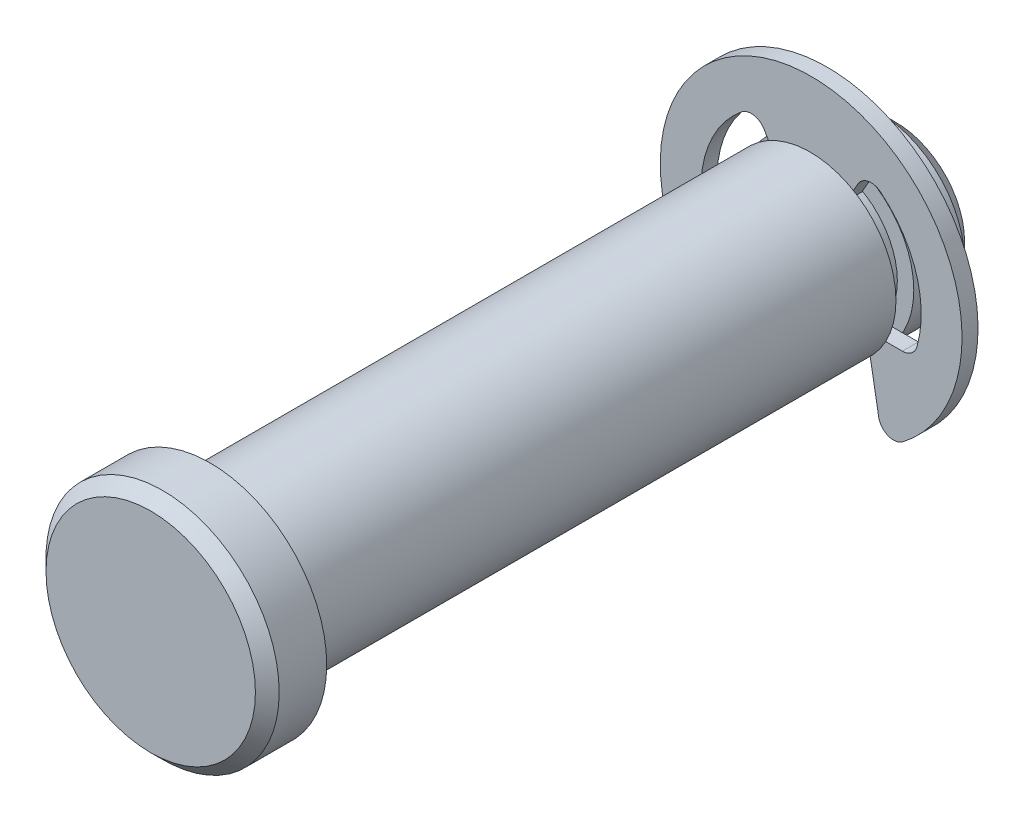
SolidWorks part; units mm, degrees
ref_plane "Front" through (0, 0, 0) normal (0, 0, 1) x (1, 0, 0)
ref_plane "Top" through (0, 0, 0) normal (0, 1, 0) x (1, 0, 0)
ref_plane "Right" through (0, 0, 0) normal (1, 0, 0) x (0, 0, -1)
sketch "Sketch2" plane through (0, 0, 0) normal (0, 0, 1) x (1, 0, 0)
  circle A0 centre (0, 0) radius 4.7625
  point P3 (0, 4.7625)
  point P4 (0, -4.7625)
  dimension "dia" = 9.525
extrude "Extrude1" add sketch "Sketch2" along normal mid plane 38.1
sketch "Sketch3" plane through (0, 0, 0) normal (1, 0, 0) x (0, 0, -1)
  line L0 (19.05, 4.7625) -> (-19.05, 4.7625) construction
  line L1 (14.2875, 4.7625) -> (15.2781, 4.7625)
  line L2 (14.2875, 4.7625) -> (14.2875, 3.8481)
  line L3 (14.2875, 3.8481) -> (15.2781, 3.8481)
  line L4 (15.2781, 4.7625) -> (15.2781, 3.8481)
  line L5 (-19.05, 4.7625) -> (-19.05, -4.7625) construction
  line L10 (15.2781, 3.8481) -> (15.2781, -3.8481) construction
  point P11 (15.2781, 0)
  point P14 (14.7828, 4.7625)
  dimension "groove wd" = 0.9906
  dimension "groove dia" = 7.6962
  dimension "usable lg" = 33.3375
revolve "Cut-Revolve1" cut sketch "Sketch3" angle 360 about axis through (0, 0, 19.05) along (0, 0, -1)
sketch "Sketch8" plane through (0, 0, 19.05) normal (0, 0, 1) x (1, 0, 0)
  circle A0 centre (0, 0) radius 6.477
  dimension "head dia" = 12.954
extrude "Extrude6" add sketch "Sketch8" along normal blind 3.302
chamfer "Chamfer2" distance 0.6604 angle 45 1 edges at (6.477, 0, 22.352)
ref_plane "Plane1" through (0, 0, -14.7828) normal (0, 0, 1) x (1, 0, 0)
sketch "Sketch4" plane through (0, 0, -14.7828) normal (0, 0, 1) x (1, 0, 0)
  line L0 (0, 3.8481) -> (0, -3.8481) construction
  circle A0 centre (0, 0) radius 8.382
  circle A1 centre (0, 0) radius 3.8481
  dimension "ring dia" = 16.764
extrude "Extrude2" add sketch "Sketch4" along normal mid plane 0.889 separate body
sketch "Sketch5" plane through (0, 0, 0) normal (0, 0, 1) x (1, 0, 0)
  line L0 (0, 8.382) -> (0, 3.8481) construction
  line L1 (-3.0575, 5.2958) -> (0, 0)
  line L2 (-5.6624, -2.3089) -> (-3.0785, -2.3089)
  line L3 (0, 0) -> (3.0575, 5.2958)
  line L4 (-3.0785, -2.3089) -> (-3.9728, -7.3807)
  line L5 (3.0785, -2.3089) -> (3.9728, -7.3807)
  line L6 (3.0785, -2.3089) -> (5.6624, -2.3089)
  arc A0 (-3.0575, 5.2958) -> (-5.6624, -2.3089) centre (0, 0) ccw
  circle A1 centre (0, 0) radius 8.382 construction
  circle A2 centre (0, 0) radius 3.8481 construction
  arc A3 (5.6624, -2.3089) -> (3.0575, 5.2958) centre (0, 0) ccw
  arc A4 (-3.9728, -7.3807) -> (3.9728, -7.3807) centre (0, 0) ccw
  circle A5 centre (0, 0) radius 3.8481 construction
  point P10 (0, 6.1151)
  dimension "D1" = 30
  dimension "D2" = 10
  dimension "D3" = 2.3089
extrude "Extrude4" cut sketch "Sketch5" against normal through all
sketch "Sketch6" plane through (0, 0, -14.3383) normal (0, 0, 1) x (1, 0, 0)
  line L0 (-1.9241, 3.3326) -> (1.9241, 3.3326)
  circle A0 centre (0, 0) radius 3.8481 construction
  arc A1 (1.9241, 3.3326) -> (-1.9241, 3.3326) centre (0, 0) ccw
extrude "Extrude5" add sketch "Sketch6" against normal up to surface (0.889 mm away) up to face at (0, 1.0514, -15.2273)
fillet "Fillet1" radius 0.8382 6 edges at (3.9728, -7.3807, -14.7828) (-3.9728, -7.3807, -14.7828) (5.6624, -2.3089, -14.7828) (3.0575, 5.2958, -14.7828) (-3.0575, 5.2958, -14.7828) (-5.6624, -2.3089, -14.7828)
chamfer "Chamfer1" distance 0.9525 angle 45 1 edges at (4.7625, 0, -19.05)
sketch "Sketch7" [suppressed] plane through (0, 0, 0) normal (1, 0, 0) x (0, 0, -1)
  line L0 (15.2273, 8.382) -> (14.3383, 8.382) construction
  line L1 (19.05, -4.7625) -> (19.05, 4.7625) construction
  line L2 (14.3383, -6.8329) -> (15.2273, -6.8329) construction
  line L3 (-22.352, 5.8166) -> (-22.352, -5.8166) construction
  point P0 (15.2781, -6.8329)
  point P1 (19.05, 4.7625)
  point P2 (-22.352, 6.477)
  point P6 (14.2875, 8.382)
  point P7 (19.05, -4.7625)
  point P12 (-19.05, 6.477)
  point P16 (14.2875, -6.8329)
equation "\"D1@Chamfer1\" = \"dia@Sketch2\" * .1"
equation "\"D1@Fillet1\" = \"ring dia@Sketch4\" * .05"
equation "\"D3@Sketch5\" = \"groove dia@Sketch3\" * .3"
equation "\"D1@Chamfer2\" = \"head ht@Extrude6\" * .2"
